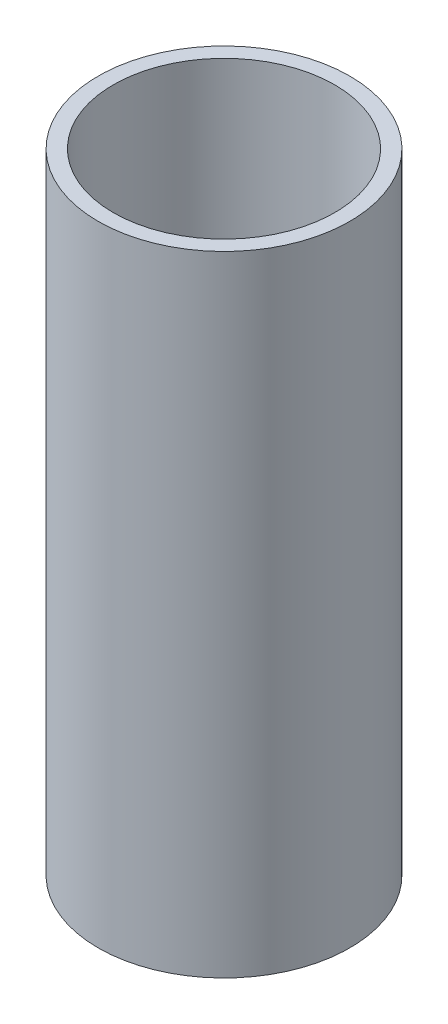
SolidWorks part; units mm, degrees
ref_plane "前基準面" through (0, 0, 0) normal (0, 0, 1) x (1, 0, 0)
ref_plane "上基準面" through (0, 0, 0) normal (0, 1, 0) x (1, 0, 0)
ref_plane "右基準面" through (0, 0, 0) normal (1, 0, 0) x (0, 0, -1)
sketch "草圖1" plane through (0, 0, 0) normal (0, 1, 0) x (1, 0, 0)
  circle A0 centre (0, 0) radius 25
  circle A1 centre (0, 0) radius 22
  dimension "D1" = 50
  dimension "D2" = 44
extrude "填料-伸長1" add sketch "草圖1" along normal blind 125
